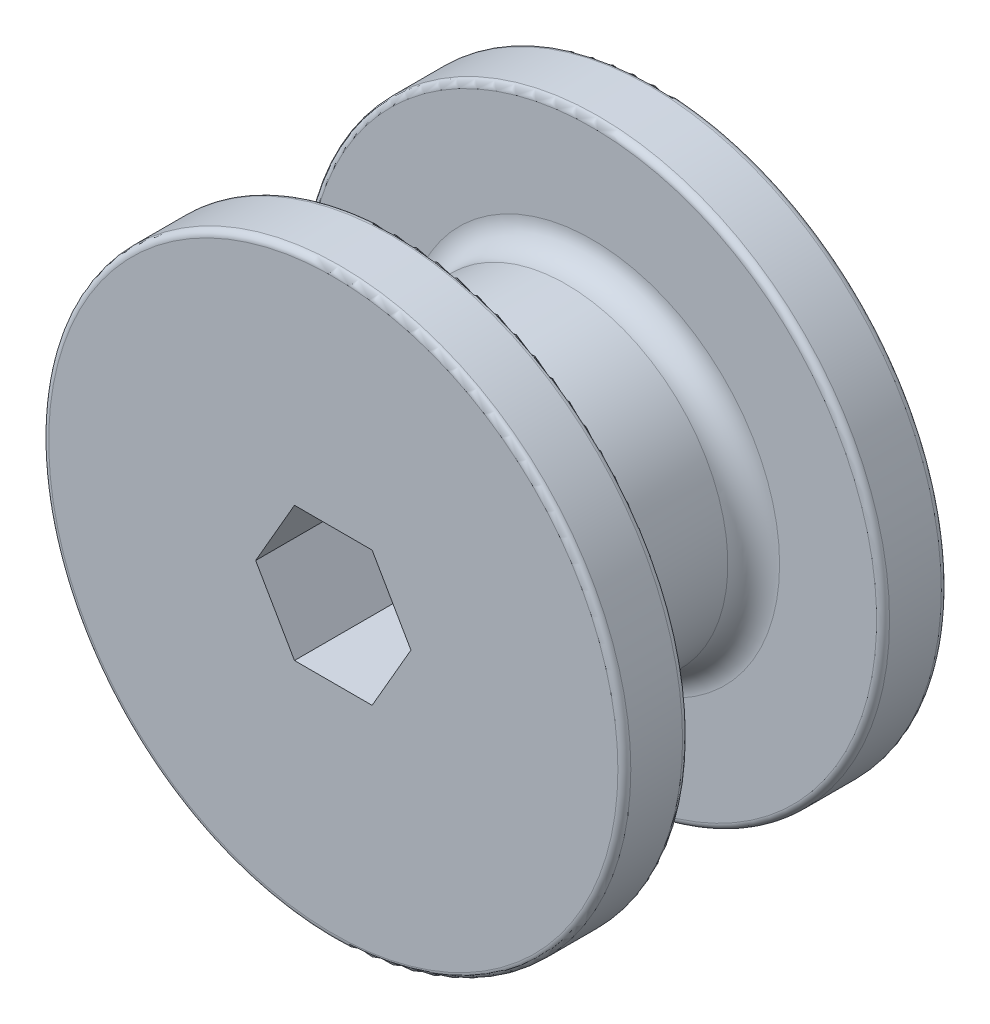
SolidWorks part; units mm, degrees
ref_plane "Front Plane" through (0, 0, 0) normal (0, 0, 1) x (1, 0, 0)
ref_plane "Top Plane" through (0, 0, 0) normal (0, 1, 0) x (1, 0, 0)
ref_plane "Right Plane" through (0, 0, 0) normal (1, 0, 0) x (0, 0, -1)
sketch "Sketch1" plane through (0, 0, 0) normal (0, 0, 1) x (1, 0, 0)
  circle A0 centre (0, 0) radius 15.875
  dimension "D1" = 31.75
extrude "Boss-Extrude1" add sketch "Sketch1" along normal blind 19.05
sketch "Sketch2" plane through (0, 0, 19.05) normal (0, 0, 1) x (1, 0, 0)
  circle A0 centre (0, 0) radius 28.575
  dimension "D1" = 57.15
extrude "Boss-Extrude2" add sketch "Sketch2" along normal blind 6.35
sketch "Sketch3" plane through (0, 0, 0) normal (0, 0, -1) x (-1, 0, 0)
  circle A0 centre (0, 0) radius 28.575
extrude "Boss-Extrude3" add sketch "Sketch3" along normal blind 6.35
sketch "Sketch4" plane through (0, 0, -6.35) normal (0, 0, -1) x (-1, 0, 0)
  line L1 (7.621, 0) -> (3.8105, 6.6)
  line L2 (3.8105, 6.6) -> (-3.8105, 6.6)
  line L3 (-3.8105, 6.6) -> (-7.621, 0)
  line L4 (-7.621, 0) -> (-3.8105, -6.6)
  line L5 (-3.8105, -6.6) -> (3.8105, -6.6)
  line L6 (3.8105, -6.6) -> (7.621, 0)
  circle A0 centre (0, 0) radius 6.6 construction
  dimension "D1" = 13.2
extrude "Cut-Extrude1" cut sketch "Sketch4" against normal through all
fillet "Fillet1" radius 2.54 2 edges at (15.875, 0, 19.05) (15.875, 0, 0)
fillet "Fillet2" radius 0.635 4 edges at (28.575, 0, 25.4) (28.575, 0, 19.05) (-28.575, 0, -6.35) (-28.575, 0, 0)
